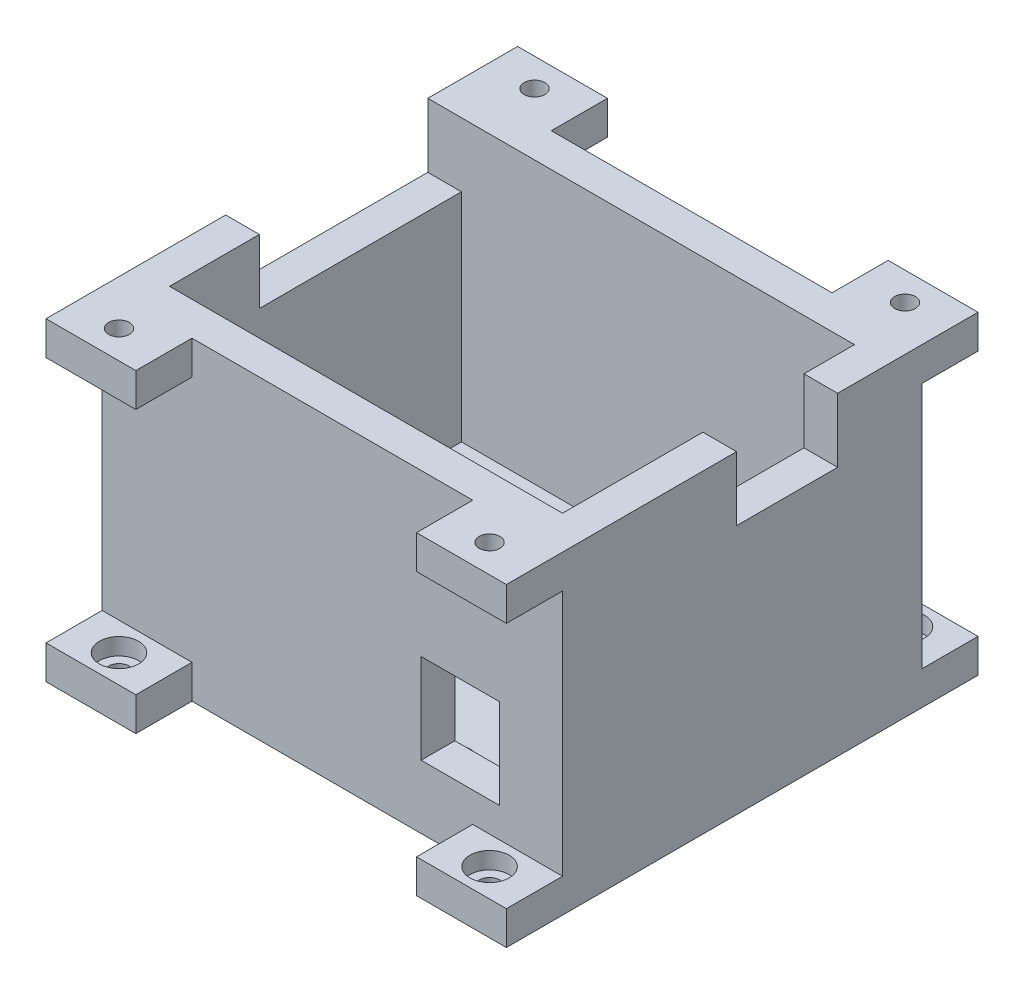
SolidWorks part; units mm, degrees
ref_plane "Спереди" through (0, 0, 0) normal (0, 0, 1) x (1, 0, 0)
ref_plane "Сверху" through (0, 0, 0) normal (0, 1, 0) x (1, 0, 0)
ref_plane "Справа" through (0, 0, 0) normal (1, 0, 0) x (0, 0, -1)
sketch "Sketch1" plane through (0, 0, 0) normal (0, 1, 0) x (1, 0, 0)
  line L1 (-8.1429, 13.9857) -> (26.8571, 13.9857)
  line L2 (-8.1429, 13.9857) -> (-8.1429, -12.0143)
  line L3 (-8.1429, -12.0143) -> (26.8571, -12.0143)
  line L4 (26.8571, 13.9857) -> (26.8571, -12.0143)
  circle A0 centre (0.5571, -10.2363) radius 0.925
  circle A1 centre (15.9241, -10.2363) radius 0.925
  circle A2 centre (15.9241, 11.6077) radius 0.925
  dimension "D3" = 1.85
  dimension "D1" = 35
  dimension "D2" = 26
  dimension "D4" = 15.367
  dimension "D5" = 8.7
  dimension "D6" = 1.778
  dimension "D7" = 21.844
extrude "Boss-Extrude1" add sketch "Sketch1" along normal blind 3
sketch "Sketch2" plane through (0, 0, 0) normal (0, -1, 0) x (1, 0, 0)
  circle A0 centre (0.5571, 10.2363) radius 1.389
  circle A1 centre (15.9241, 10.2363) radius 1.389
  circle A2 centre (15.9241, -11.6077) radius 1.389
extrude "Cut-Extrude4" cut sketch "Sketch2" against normal blind 1.5
sketch "Sketch3" plane through (0, 3, 0) normal (0, 1, 0) x (1, 0, 0)
  line L1 (-8.1429, 13.9857) -> (26.8571, 13.9857)
  line L2 (-8.1429, 13.9857) -> (-8.1429, -12.0143)
  line L3 (-8.1429, -12.0143) -> (26.8571, -12.0143)
  line L4 (26.8571, 13.9857) -> (26.8571, -12.0143)
  line L5 (-11.1429, 16.9857) -> (29.8571, 16.9857)
  line L6 (-11.1429, 16.9857) -> (-11.1429, -15.0143)
  line L7 (-11.1429, -15.0143) -> (29.8571, -15.0143)
  line L8 (29.8571, 16.9857) -> (29.8571, -15.0143)
  dimension "D1" = 3
  dimension "D2" = 3
  dimension "D3" = 3
  dimension "D4" = 3
extrude "Boss-Extrude2" add sketch "Sketch3" along normal blind 25 and the other way blind 3
sketch "Sketch4" plane through (-8.1429, 0, 0) normal (1, 0, 0) x (0, 0, -1)
  line L1 (13.9857, 28) -> (-4.0143, 28)
  line L2 (13.9857, 28) -> (13.9857, 22.29)
  line L3 (13.9857, 22.29) -> (-4.0143, 22.29)
  line L4 (-4.0143, 28) -> (-4.0143, 22.29)
  dimension "D1" = 5.71
  dimension "D2" = 18
extrude "Cut-Extrude5" cut sketch "Sketch4" against normal blind 25
sketch "Sketch5" plane through (26.8571, 0, 0) normal (-1, 0, 0) x (0, 0, 1)
  line L0 (12.0143, 28) -> (-13.9857, 28) construction
  line L1 (-9.4857, 28) -> (-0.4857, 28)
  line L2 (-9.4857, 28) -> (-9.4857, 22.29)
  line L3 (-9.4857, 22.29) -> (-0.4857, 22.29)
  line L4 (-0.4857, 28) -> (-0.4857, 22.29)
  line L5 (-13.9857, 28) -> (4.0143, 28) construction
  point P9 (-4.9857, 28)
  dimension "D1" = 9
  dimension "D2" = 18
  dimension "D3" = 5.71
extrude "Cut-Extrude6" cut sketch "Sketch5" against normal blind 25
sketch "Sketch6" plane through (0, 3, 0) normal (0, 1, 0) x (1, 0, 0)
  line L1 (-0.8139, -5.7363) -> (2.1861, -5.7363)
  line L2 (-0.8139, -5.7363) -> (-0.8139, -8.7363)
  line L3 (-0.8139, -8.7363) -> (2.1861, -8.7363)
  line L4 (2.1861, -5.7363) -> (2.1861, -8.7363)
  circle A0 centre (0.5571, -10.2363) radius 0.925 construction
  dimension "D1" = 3
  dimension "D2" = 3
  dimension "D3" = 1.5
extrude "Cut-Extrude7" cut sketch "Sketch6" against normal blind 25
sketch "Sketch8" plane through (0, 0, 15.0143) normal (0, 0, 1) x (1, 0, 0)
  line L1 (17.2652, 13.6532) -> (24.2652, 13.6532)
  line L2 (17.2652, 13.6532) -> (17.2652, 5.6532)
  line L3 (17.2652, 5.6532) -> (24.2652, 5.6532)
  line L4 (24.2652, 13.6532) -> (24.2652, 5.6532)
  dimension "D1" = 8
  dimension "D2" = 7
extrude "Cut-Extrude8" cut sketch "Sketch8" against normal blind 25
sketch "Sketch9" plane through (0, 0, -16.9857) normal (0, 0, -1) x (-1, 0, 0)
  line L1 (11.1429, 0) -> (3.1429, 0)
  line L2 (11.1429, 0) -> (11.1429, 3)
  line L3 (11.1429, 3) -> (3.1429, 3)
  line L4 (3.1429, 0) -> (3.1429, 3)
  line L5 (-29.8571, 0) -> (-21.8571, 0)
  line L6 (-29.8571, 0) -> (-29.8571, 3)
  line L7 (-29.8571, 3) -> (-21.8571, 3)
  line L8 (-21.8571, 0) -> (-21.8571, 3)
  dimension "D1" = 8
  dimension "D2" = 3
extrude "Boss-Extrude3" add sketch "Sketch9" along normal blind 5
sketch "Sketch10" plane through (0, 0, 15.0143) normal (0, 0, 1) x (1, 0, 0)
  line L1 (-11.1429, 0) -> (-3.1429, 0)
  line L2 (-11.1429, 0) -> (-11.1429, 3)
  line L3 (-11.1429, 3) -> (-3.1429, 3)
  line L4 (-3.1429, 0) -> (-3.1429, 3)
  line L5 (29.8571, 0) -> (21.8571, 0)
  line L6 (29.8571, 0) -> (29.8571, 3)
  line L7 (29.8571, 3) -> (21.8571, 3)
  line L8 (21.8571, 0) -> (21.8571, 3)
  dimension "D1" = 8
  dimension "D2" = 3
extrude "Boss-Extrude4" add sketch "Sketch10" along normal blind 5
sketch "Sketch11" plane through (0, 3, 0) normal (0, 1, 0) x (1, 0, 0)
  line L0 (-11.1429, -20.0143) -> (-11.1429, -15.0143) construction
  line L1 (-3.1429, -20.0143) -> (-11.1429, -20.0143) construction
  line L3 (-11.1429, 21.9857) -> (-3.1429, 21.9857) construction
  line L5 (29.8571, 21.9857) -> (29.8571, 16.9857) construction
  circle A0 centre (-7.1429, -17.5143) radius 0.925
  circle A1 centre (25.8571, -17.5143) radius 0.925
  circle A2 centre (25.8571, 19.4857) radius 0.925
  circle A3 centre (-7.1429, 19.4857) radius 0.925
  dimension "D1" = 1.85
  dimension "D2" = 4
  dimension "D3" = 2.5
  dimension "D4" = 2.5
  dimension "D5" = 4
extrude "Cut-Extrude9" cut sketch "Sketch11" against normal blind 5
sketch "Sketch12" plane through (0, 3, 0) normal (0, 1, 0) x (1, 0, 0)
  circle A0 centre (-7.1429, -17.5143) radius 1.75
  circle A1 centre (-7.1429, 19.4857) radius 1.75
  circle A2 centre (25.8571, 19.4857) radius 1.75
  circle A3 centre (25.8571, -17.5143) radius 1.75
  dimension "D1" = 3.5
extrude "Cut-Extrude10" cut sketch "Sketch12" against normal blind 1.5
sketch "Sketch13" plane through (0, 0, 15.0143) normal (0, 0, 1) x (1, 0, 0)
  line L1 (29.8571, 28) -> (21.8571, 28)
  line L2 (29.8571, 28) -> (29.8571, 25)
  line L3 (29.8571, 25) -> (21.8571, 25)
  line L4 (21.8571, 28) -> (21.8571, 25)
  line L5 (-11.1429, 28) -> (-3.1429, 28)
  line L6 (-11.1429, 28) -> (-11.1429, 25)
  line L7 (-11.1429, 25) -> (-3.1429, 25)
  line L8 (-3.1429, 28) -> (-3.1429, 25)
  dimension "D1" = 8
  dimension "D2" = 8
  dimension "D3" = 3
  dimension "D4" = 3
extrude "Boss-Extrude5" add sketch "Sketch13" along normal blind 5
sketch "Sketch14" plane through (0, 0, -16.9857) normal (0, 0, -1) x (-1, 0, 0)
  line L1 (-29.8571, 28) -> (-21.8571, 28)
  line L2 (-29.8571, 28) -> (-29.8571, 25)
  line L3 (-29.8571, 25) -> (-21.8571, 25)
  line L4 (-21.8571, 28) -> (-21.8571, 25)
  line L5 (11.1429, 28) -> (3.1429, 28)
  line L6 (11.1429, 28) -> (11.1429, 25)
  line L7 (11.1429, 25) -> (3.1429, 25)
  line L8 (3.1429, 28) -> (3.1429, 25)
  dimension "D1" = 8
  dimension "D2" = 8
  dimension "D3" = 3
  dimension "D4" = 3
extrude "Boss-Extrude6" add sketch "Sketch14" along normal blind 5
sketch "Sketch15" plane through (0, 25, 0) normal (0, -1, 0) x (1, 0, 0)
  line L1 (-3.1429, -21.9857) -> (-11.1429, -21.9857) construction
  line L3 (29.8571, -9.4857) -> (29.8571, -21.9857) construction
  circle A0 centre (25.8571, 17.5143) radius 0.925
  circle A1 centre (-7.1429, 17.5143) radius 0.925
  circle A2 centre (25.8571, -19.4857) radius 0.925
  circle A3 centre (-7.1429, -19.4857) radius 0.925
  dimension "D3" = 1.85
  dimension "D1" = 2.5
  dimension "D2" = 4
extrude "Cut-Extrude11" cut sketch "Sketch15" against normal blind 5
sketch "Sketch17" plane through (0, 25, 0) normal (0, -1, 0) x (1, 0, 0)
  circle A1 centre (25.8571, -19.4857) radius 1.75
  circle A3 centre (25.8571, 17.5143) radius 1.75
  circle A4 centre (-7.1429, 17.5143) radius 1.75
  circle A5 centre (-7.1429, -19.4857) radius 1.75
  dimension "D1" = 3.5
extrude "Cut-Extrude13" cut sketch "Sketch17" against normal blind 1.5
